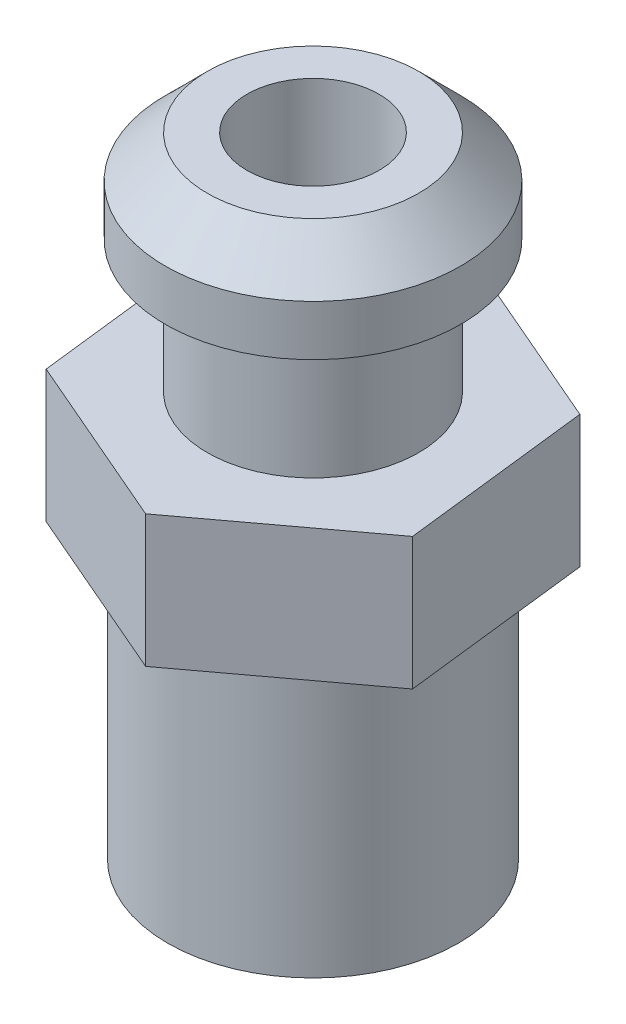
SolidWorks part; units mm, degrees
material "Plain Carbon Steel"
ref_plane "Front Plane" through (0, 0, 0) normal (0, 0, 1) x (1, 0, 0)
ref_plane "Top Plane" through (0, 0, 0) normal (0, 1, 0) x (1, 0, 0)
ref_plane "Right Plane" through (0, 0, 0) normal (1, 0, 0) x (0, 0, -1)
sketch "Sketch1" plane through (0, 0, 0) normal (1, 0, 0) x (0, 0, -1)
  line L0 (0, 0) -> (0, 13.716)
  line L1 (0, 13.716) -> (2.032, 13.716)
  line L2 (2.032, 13.716) -> (2.8398, 12.9082)
  line L3 (2.8398, 12.9082) -> (2.8398, 11.938)
  line L4 (2.8398, 11.938) -> (2.032, 11.938)
  line L5 (2.032, 11.938) -> (2.032, 9.398)
  line L6 (2.032, 9.398) -> (4.8689, 9.398)
  line L7 (4.8689, 9.398) -> (4.8689, 6.858)
  line L8 (0, 0) -> (2.794, 1.6131)
  line L9 (4.8689, 6.858) -> (2.794, 6.858)
  line L10 (2.794, 6.858) -> (2.794, 1.6131)
  line L11 (2.794, 6.858) -> (-2.4224, 6.858) construction
  dimension "D1" = 2.794
  dimension "D2" = 60
  dimension "D3" = 2.032
  dimension "D4" = 2.54
  dimension "D5" = 2.54
  dimension "D6" = 1.778
  dimension "D7" = 135
revolve "Revolve2" add sketch "Sketch1" angle 360 about L0
sketch "Sketch2" plane through (0, 9.398, 0) normal (0, 1, 0) x (1, 0, 0)
  line L1 (3.366, -1.4529) -> (2.9412, 2.1886)
  line L2 (2.9412, 2.1886) -> (-0.4248, 3.6415)
  line L3 (-0.4248, 3.6415) -> (-3.366, 1.4529)
  line L4 (-3.366, 1.4529) -> (-2.9412, -2.1886)
  line L5 (-2.9412, -2.1886) -> (0.4248, -3.6415)
  line L6 (0.4248, -3.6415) -> (3.366, -1.4529)
  circle A0 centre (0, 0) radius 3.175 construction
  dimension "D1" = 6.35
extrude "Cut-Extrude1" cut sketch "Sketch2" against normal blind 2.54 flip side to cut
sketch "Sketch3" plane through (0, 13.716, 0) normal (0, 1, 0) x (1, 0, 0)
  circle A0 centre (0, 0) radius 1.27
  dimension "D1" = 2.54
extrude "Cut-Extrude2" cut sketch "Sketch3" against normal blind 11.43
sketch "Sketch4" plane through (0, 0, 0) normal (1, 0, 0) x (0, 0, -1)
  circle A0 centre (0, 3.792) radius 0.635
  dimension "D1" = 1.27
extrude "Cut-Extrude3" cut sketch "Sketch4" against normal blind 11.43
